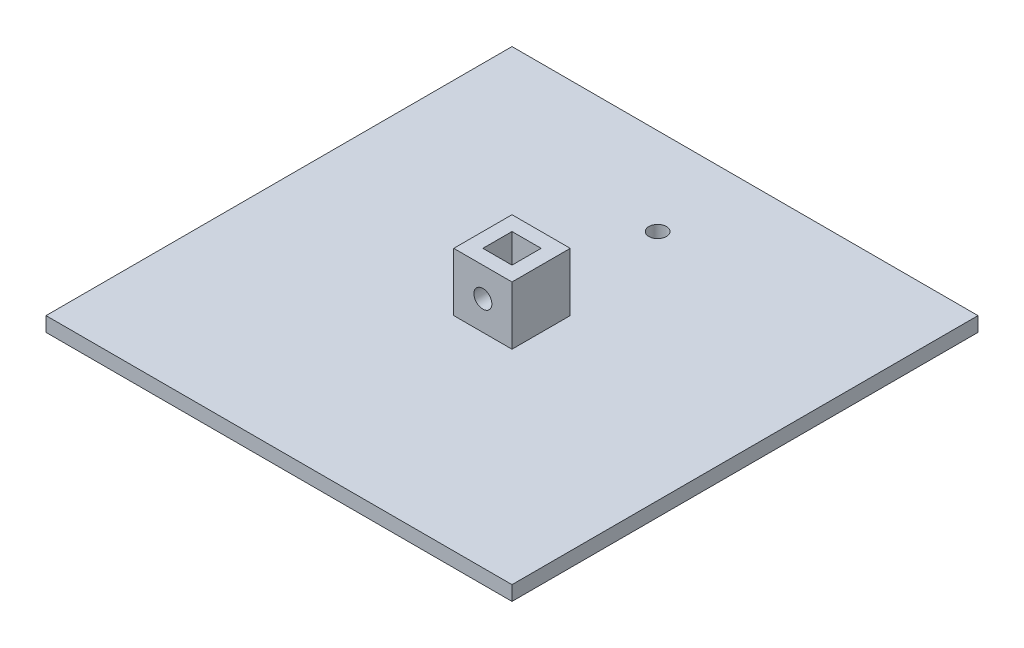
SolidWorks part; units mm, degrees
ref_plane "Front Plane" through (0, 0, 0) normal (0, 0, 1) x (1, 0, 0)
ref_plane "Top Plane" through (0, 0, 0) normal (0, 1, 0) x (1, 0, 0)
ref_plane "Right Plane" through (0, 0, 0) normal (1, 0, 0) x (0, 0, -1)
sketch "Sketch1" plane through (0, 0, 0) normal (0, 1, 0) x (1, 0, 0)
  line L1 (101.6, -101.6) -> (-101.6, -101.6)
  line L2 (101.6, -101.6) -> (101.6, 101.6)
  line L3 (101.6, 101.6) -> (-101.6, 101.6)
  line L4 (-101.6, -101.6) -> (-101.6, 101.6)
  line L5 (101.6, -101.6) -> (-101.6, 101.6) construction
  line L6 (101.6, 101.6) -> (-101.6, -101.6) construction
  point P0 (0, 0)
  dimension "8" = 203.2
  dimension "D2" = 203.2
extrude "Boss-Extrude1" add sketch "Sketch1" along normal blind 6.35
sketch "Sketch2" plane through (0, 0, 0) normal (0, 1, 0) x (1, 0, 0)
  line L1 (-12.7, -12.7) -> (12.7, -12.7)
  line L2 (-12.7, -12.7) -> (-12.7, 12.7)
  line L3 (-12.7, 12.7) -> (12.7, 12.7)
  line L4 (12.7, -12.7) -> (12.7, 12.7)
  line L5 (-12.7, -12.7) -> (12.7, 12.7) construction
  line L6 (-12.7, 12.7) -> (12.7, -12.7) construction
  line L7 (-6.35, -6.35) -> (6.35, -6.35)
  line L8 (-6.35, -6.35) -> (-6.35, 6.35)
  line L9 (-6.35, 6.35) -> (6.35, 6.35)
  line L10 (6.35, -6.35) -> (6.35, 6.35)
  line L11 (-6.35, -6.35) -> (6.35, 6.35) construction
  line L12 (-6.35, 6.35) -> (6.35, -6.35) construction
  point P0 (0, 0)
  point P6 (0, 0)
  dimension "D1" = 25.4
  dimension "D2" = 25.4
  dimension "D3" = 12.7
  dimension "D4" = 12.7
extrude "Boss-Extrude2" add sketch "Sketch2" along normal blind 31.75
sketch "Sketch3" plane through (0, 0, 12.7) normal (0, 0, 1) x (1, 0, 0)
  line L0 (-101.6, 6.35) -> (101.6, 6.35) construction
  line L1 (-12.7, 31.75) -> (-12.7, 6.35) construction
  circle A0 centre (0, 19.05) radius 3.9063
  dimension "D1" = 7.8126
  dimension "D2" = 12.7
  dimension "D3" = 12.7
extrude "Cut-Extrude1" cut sketch "Sketch3" against normal blind 25.4
sketch "Sketch4" plane through (0, 6.35, 0) normal (0, 1, 0) x (1, 0, 0)
  line L0 (101.6, 101.6) -> (-101.6, 101.6) construction
  line L1 (101.6, -101.6) -> (101.6, 101.6) construction
  circle A0 centre (0, 63.5) radius 3.81
  dimension "D3" = 7.62
  dimension "D1" = 38.1
  dimension "D2" = 101.6
extrude "Cut-Extrude2" cut sketch "Sketch4" against normal blind 25.4
